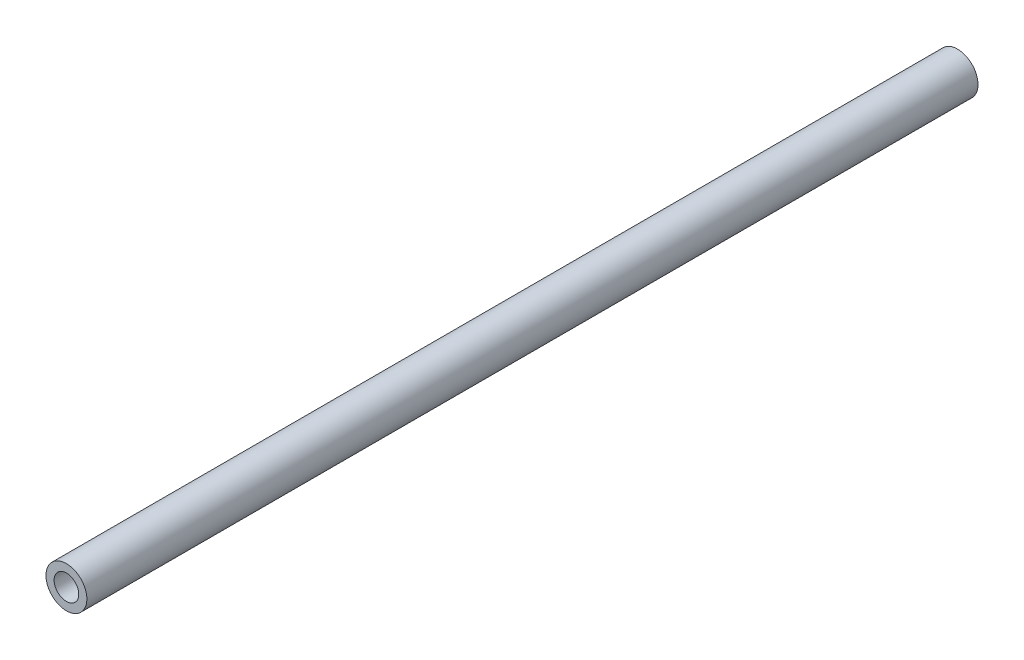
SolidWorks part; units mm, degrees
ref_plane "Front Plane" through (0, 0, 0) normal (0, 0, 1) x (1, 0, 0)
ref_plane "Top Plane" through (0, 0, 0) normal (0, 1, 0) x (1, 0, 0)
ref_plane "Right Plane" through (0, 0, 0) normal (1, 0, 0) x (0, 0, -1)
sketch "Sketch1" plane through (0, 0, 0) normal (0, 0, 1) x (1, 0, 0)
  circle A0 centre (-14.7939, 11.5976) radius 12.8268
  circle A1 centre (-14.7939, 11.5976) radius 7.7314
extrude "Boss-Extrude1" add sketch "Sketch1" along normal blind 558.8
